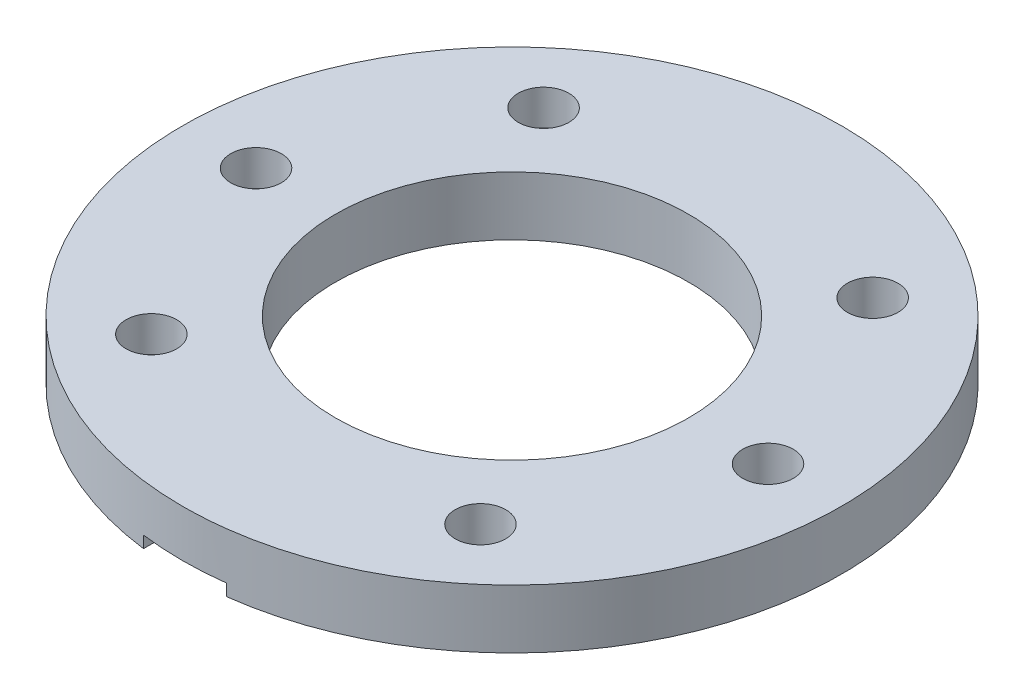
SolidWorks part; units mm, degrees
ref_plane "前视基准面" through (0, 0, 0) normal (0, 0, 1) x (1, 0, 0)
ref_plane "上视基准面" through (0, 0, 0) normal (0, 1, 0) x (1, 0, 0)
ref_plane "右视基准面" through (0, 0, 0) normal (1, 0, 0) x (0, 0, -1)
sketch "草图1" plane through (0, 0, 0) normal (0, 1, 0) x (1, 0, 0)
  circle A0 centre (0, 0) radius 28
  circle A1 centre (13.9806, -16.6615) radius 2.15
  circle A2 centre (13.9806, 16.6615) radius 2.15
  circle A3 centre (21.75, 0) radius 2.15
  circle A4 centre (-13.9806, -16.6615) radius 2.15
  circle A5 centre (-21.75, 0) radius 2.15
  circle A6 centre (-13.9806, 16.6615) radius 2.15
  circle A9 centre (0, 0) radius 15
extrude "凸台-拉伸1" add sketch "草图1" along normal blind 5
sketch "草图2" plane through (0, 0, 0) normal (0, 1, 0) x (1, 0, 0)
  line L4 (3.5355, -26.5355) -> (3.5355, -27.7759)
  line L6 (-3.5355, -26.5355) -> (-3.5355, -27.7759)
  arc A4 (3.5355, -26.5355) -> (-3.5355, -26.5355) centre (0, -23) ccw
  arc A5 (-3.5355, -27.7759) -> (3.5355, -27.7759) centre (0, 0) ccw
extrude "切除-拉伸3" cut sketch "草图2" along normal blind 1
sketch "草图5" plane through (0, 0, 0) normal (0, -1, 0) x (1, 0, 0)
  circle A0 centre (-13.9806, 16.6615) radius 5
  circle A2 centre (-21.75, 0) radius 5
  circle A3 centre (-13.9806, -16.6615) radius 5
  circle A4 centre (13.9806, -16.6615) radius 5
  circle A5 centre (21.75, 0) radius 5
  circle A6 centre (13.9806, 16.6615) radius 5
extrude "切除-拉伸5" cut sketch "草图5" against normal blind 2 contours A3 | A2 | A0
sketch "草图6" plane through (0, 1, 0) normal (0, -1, 0) x (1, 0, 0)
  circle A0 centre (0, 23) radius 4.5
extrude "切除-拉伸6" cut sketch "草图6" against normal blind 1
ref_axis "基准轴1" through (0, 2, 23) along (0, -1, 0)
ref_plane "基准面1" through (0, 0, 0) normal (-1, 0, 0) x (0, -1, 0)
sketch "草图7" plane through (0, 0, 0) normal (-1, 0, 0) x (0, -1, 0)
  line L0 (-2, 23) -> (-1, 23)
  line L2 (-2, 23) -> (0.5473, 23) construction
  line L3 (-2, 23) -> (-2, 27.5)
  line L4 (-2, 27.5) -> (-1, 23)
revolve "旋转1" add sketch "草图7" angle 360 about axis through (0, 2, 23) along (0, -1, 0)
